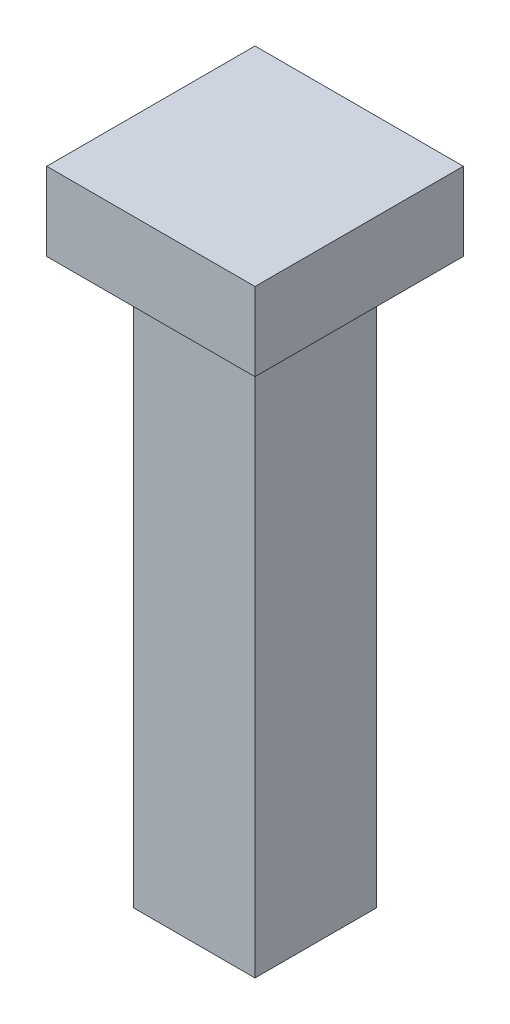
SolidWorks part; units mm, degrees
ref_plane "Front Plane" through (0, 0, 0) normal (0, 0, 1) x (1, 0, 0)
ref_plane "Top Plane" through (0, 0, 0) normal (0, 1, 0) x (1, 0, 0)
ref_plane "Right Plane" through (0, 0, 0) normal (1, 0, 0) x (0, 0, -1)
sketch "Sketch1" plane through (0, 0, 0) normal (0, 1, 0) x (1, 0, 0)
  line L1 (0, 0) -> (3.556, 0)
  line L2 (0, 0) -> (0, -3.556)
  line L3 (0, -3.556) -> (3.556, -3.556)
  line L4 (3.556, 0) -> (3.556, -3.556)
  dimension "D1" = 3.556
  dimension "D2" = 3.556
extrude "Boss-Extrude1" add sketch "Sketch1" along normal blind 16.51
sketch "Sketch2" plane through (0, 16.51, 0) normal (0, 1, 0) x (1, 0, 0)
  line L8 (-1.27, 1.27) -> (-1.27, -4.826)
  line L9 (-1.27, -4.826) -> (4.826, -4.826)
  line L10 (4.826, -4.826) -> (4.826, 1.27)
  line L11 (4.826, 1.27) -> (-1.27, 1.27)
  line L12 (-1.27, 1.27) -> (-1.27, -4.826)
  line L13 (-1.27, -4.826) -> (4.826, -4.826)
  line L14 (4.826, -4.826) -> (4.826, 1.27)
  line L15 (4.826, 1.27) -> (-1.27, 1.27)
  dimension "D1" = 1.27
extrude "Boss-Extrude2" add sketch "Sketch2" along normal blind 2.286
